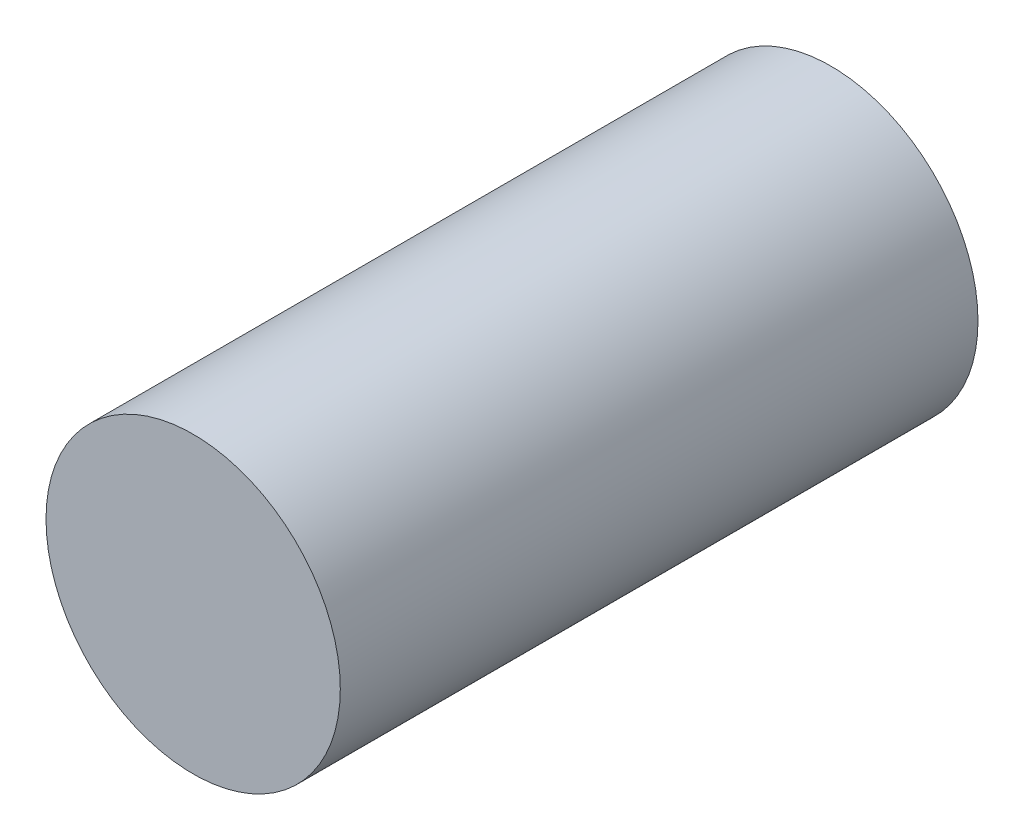
SolidWorks part; units mm, degrees
ref_plane "Front Plane" through (0, 0, 0) normal (0, 0, 1) x (1, 0, 0)
ref_plane "Top Plane" through (0, 0, 0) normal (0, 1, 0) x (1, 0, 0)
ref_plane "Right Plane" through (0, 0, 0) normal (1, 0, 0) x (0, 0, -1)
sketch "Sketch2" plane through (0, 0, 0) normal (0, 0, 1) x (1, 0, 0)
  circle A0 centre (0, 0) radius 0.3
extrude "Boss-Extrude2" add sketch "Sketch2" along normal blind 1.3
